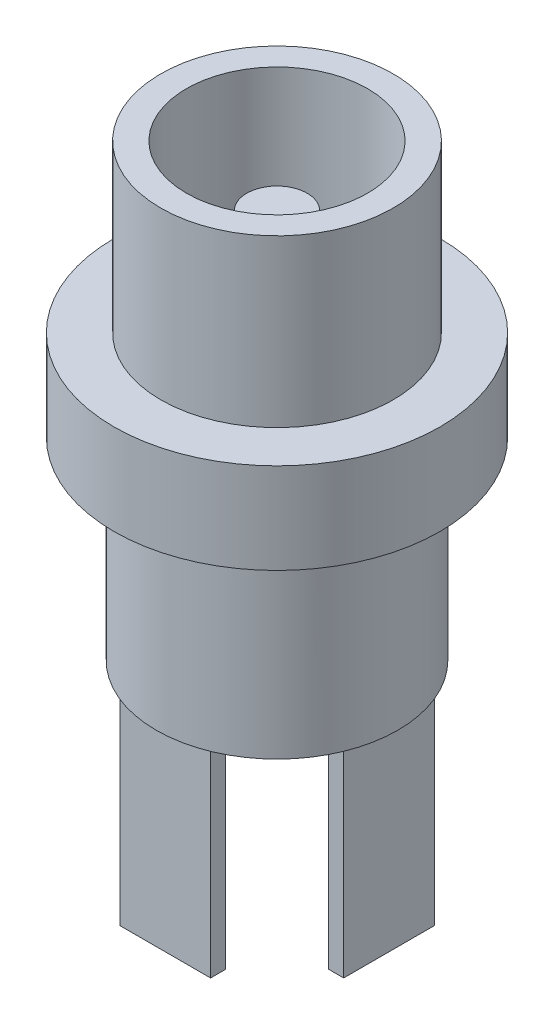
SolidWorks part; units mm, degrees
ref_plane "Plan de face" through (0, 0, 0) normal (0, 0, 1) x (1, 0, 0)
ref_plane "Plan de dessus" through (0, 0, 0) normal (0, 1, 0) x (1, 0, 0)
ref_plane "Plan de droite" through (0, 0, 0) normal (1, 0, 0) x (0, 0, -1)
sketch "Esquisse1" plane through (0, 0, 0) normal (0, 1, 0) x (1, 0, 0)
  circle A0 centre (0, 0) radius 5.4
  dimension "D1" = 10.8
extrude "Boss.-Extru.1" add sketch "Esquisse1" along normal blind 3
sketch "Esquisse2" plane through (0, 3, 0) normal (0, 1, 0) x (1, 0, 0)
  circle A0 centre (0, 0) radius 3.85
  dimension "D1" = 7.7
extrude "Boss.-Extru.2" add sketch "Esquisse2" along normal blind 5.5
sketch "Esquisse3" plane through (0, 0, 0) normal (0, -1, 0) x (1, 0, 0)
  circle A0 centre (0, 0) radius 4
  dimension "D1" = 8
extrude "Boss.-Extru.3" add sketch "Esquisse3" along normal blind 6.4
sketch "Esquisse4" plane through (0, -6.4, 0) normal (0, -1, 0) x (1, 0, 0)
  line L0 (-0.8235, 0) -> (0.7226, 0) construction
  line L1 (-1.4949, -3.7036) -> (1.5051, -3.7036)
  line L2 (-1.4949, -3.7036) -> (-1.4949, -3.2036)
  line L3 (-1.4949, -3.2036) -> (1.5051, -3.2036)
  line L4 (1.5051, -3.7036) -> (1.5051, -3.2036)
  line L5 (1.5051, 3.7036) -> (1.5051, 3.2036)
  line L6 (-1.4949, 3.2036) -> (1.5051, 3.2036)
  line L7 (-1.4949, 3.7036) -> (-1.4949, 3.2036)
  line L8 (-1.4949, 3.7036) -> (1.5051, 3.7036)
  line L10 (3.7081, -1.5) -> (3.2081, -1.5)
  line L11 (3.7081, -1.5) -> (3.7081, 1.5)
  line L12 (3.7081, 1.5) -> (3.2081, 1.5)
  line L13 (3.2081, -1.5) -> (3.2081, 1.5)
  circle A1 centre (0, 0) radius 4 construction
  dimension "D1" = 3
  dimension "D2" = 0.5
  dimension "D3" = 3
  dimension "D4" = 0.5
  dimension "D5" = 1.5
extrude "Boss.-Extru.4" add sketch "Esquisse4" along normal blind 6.5
sketch "Esquisse5" plane through (0, 8.5, 0) normal (0, 1, 0) x (1, 0, 0)
  circle A0 centre (0, 0) radius 3
  dimension "D1" = 6
extrude "Enlèv. mat.-Extru.1" cut sketch "Esquisse5" against normal blind 10
sketch "Esquisse6" plane through (0, -1.5, 0) normal (0, 1, 0) x (1, 0, 0)
  circle A0 centre (0, 0) radius 1
  dimension "D1" = 2
extrude "Boss.-Extru.5" add sketch "Esquisse6" along normal blind 8
